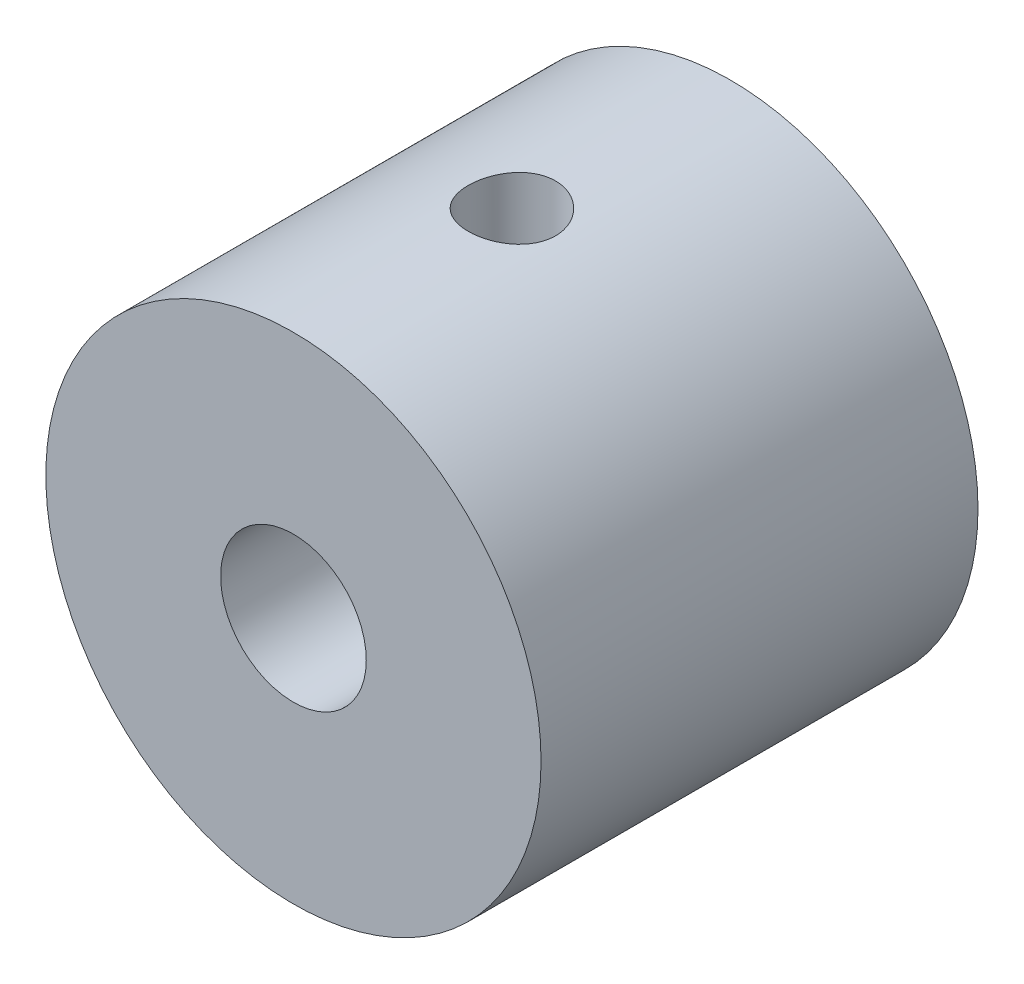
SolidWorks part; units mm, degrees
ref_plane "Alzado" through (0, 0, 0) normal (0, 0, 1) x (1, 0, 0)
ref_plane "Planta" through (0, 0, 0) normal (0, 1, 0) x (1, 0, 0)
ref_plane "Vista lateral" through (0, 0, 0) normal (1, 0, 0) x (0, 0, -1)
sketch "Croquis1" plane through (0, 0, 0) normal (0, 0, 1) x (1, 0, 0)
  circle A0 centre (0, 0) radius 8.5
  circle A1 centre (0, 0) radius 2.5
  dimension "D1" = 17
  dimension "D2" = 5
extrude "Saliente-Extruir1" add sketch "Croquis1" along normal blind 15
sketch "Croquis2" plane through (0, 0, 0) normal (0, 1, 0) x (1, 0, 0)
  line L0 (-8.5, 0) -> (-8.5, -15) construction
  circle A0 centre (0, -7.5) radius 1.5
  point P6 (-8.5, -7.5)
  point P7 (0, 0)
  dimension "D1" = 3
extrude "Cortar-Extruir1" cut sketch "Croquis2" against normal through all both and the other way through all
